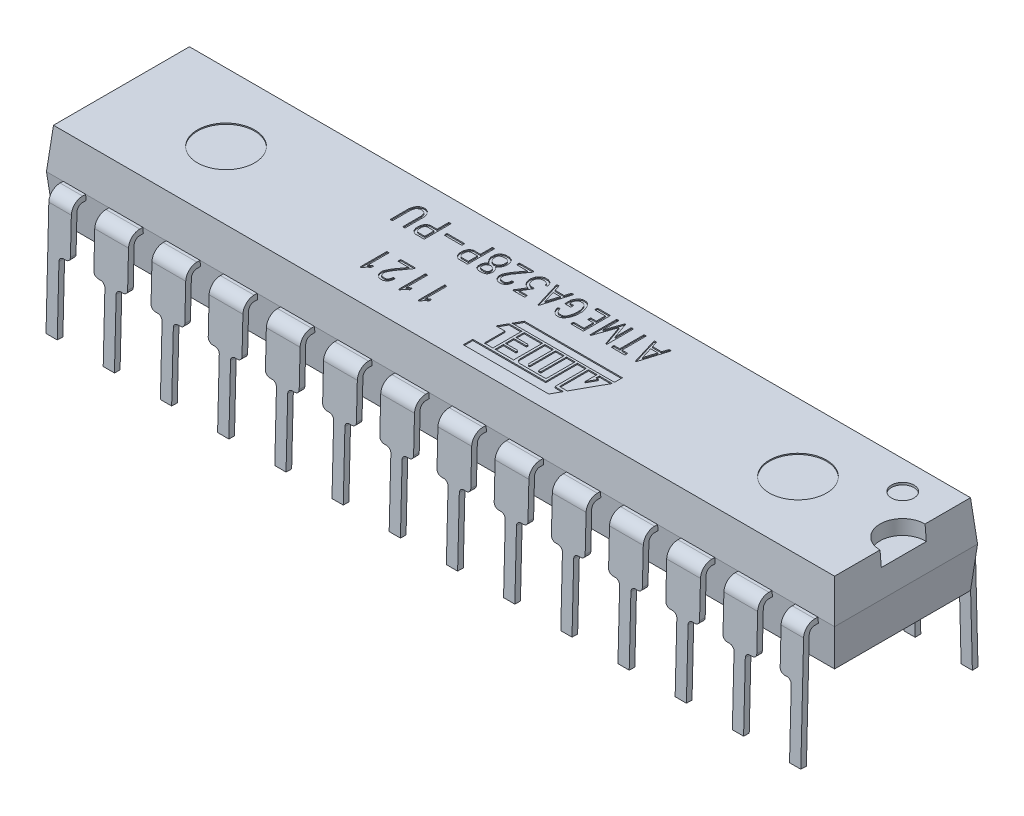
SolidWorks part; units mm, degrees
material "Pure Silver"
ref_plane "Front Plane" through (0, 0, 0) normal (0, 0, 1) x (1, 0, 0)
ref_plane "Top Plane" through (0, 0, 0) normal (0, 1, 0) x (1, 0, 0)
ref_plane "Right Plane" through (0, 0, 0) normal (1, 0, 0) x (0, 0, -1)
sketch "Sketch1" plane through (0, 0, 0) normal (1, 0, 0) x (0, 0, -1)
  line L0 (-3.935, -3.18) -> (-3.81, 1.8075)
  line L1 (-3.3102, 2.295) -> (3.3102, 2.295)
  line L2 (3.81, 1.8075) -> (3.935, -3.18)
  line L4 (55, 0) -> (-55, 0) construction
  line L5 (0, 4.893) -> (0, -4.893) construction
  arc A0 (3.3102, 2.295) -> (3.81, 1.8075) centre (3.3102, 1.795) cw
  arc A1 (-3.81, 1.8075) -> (-3.3102, 2.295) centre (-3.3102, 1.795) cw
  dimension "D1" = 0.5
  dimension "D2" = 7.62
  dimension "D3" = 3.81
  dimension "D4" = 3.18
  dimension "D5" = 2.295
  dimension "D6" = 7.87
  dimension "D7" = 3.935
extrude "Extrude-Thin1" add sketch "Sketch1" along normal mid plane 33.52 thin
sketch "Sketch2" plane through (0, 0, 0) normal (0, 0, 1) x (1, 0, 0)
  line L0 (-3.56, -3.5) -> (-3.56, -0.2)
  line L1 (-6.1, -3.5) -> (-6.1, -0.2)
  line L2 (4.3285, 0) -> (-4.3285, 0) construction
  line L3 (-1.52, -0.2) -> (-1.52, -3.5)
  line L4 (-3.56, -3.5) -> (-1.52, -3.5)
  line L5 (-1.02, -3.5) -> (-1.02, -0.2)
  line L6 (1.02, -0.2) -> (1.02, -3.5)
  line L7 (-1.02, -3.5) -> (1.02, -3.5)
  line L8 (1.52, -3.5) -> (1.52, -0.2)
  line L9 (3.56, -0.2) -> (3.56, -3.5)
  line L10 (1.52, -3.5) -> (3.56, -3.5)
  line L11 (-4.06, -0.2) -> (-4.06, -3.5)
  line L12 (-5.9, 0) -> (-5.8, 0)
  line L13 (0, -3.0147) -> (0, 3.0147) construction
  line L14 (-3.36, 0) -> (-3.26, 0)
  line L15 (-3.06, 0.2) -> (-3.06, 2.295)
  line L16 (16.76, 2.295) -> (-16.76, 2.295) construction
  line L17 (-3.06, 2.295) -> (-2.02, 2.295)
  line L18 (-2.02, 2.295) -> (-2.02, 0.2)
  line L19 (-0.52, 0.2) -> (-0.52, 2.295)
  line L20 (-0.52, 2.295) -> (0.52, 2.295)
  line L21 (0.52, 2.295) -> (0.52, 0.2)
  line L22 (2.02, 0.2) -> (2.02, 2.295)
  line L23 (2.02, 2.295) -> (3.06, 2.295)
  line L24 (3.06, 2.295) -> (3.06, 0.2)
  line L25 (-5.6, 0.2) -> (-5.6, 2.295)
  line L26 (-1.82, 0) -> (-1.72, 0)
  line L27 (-4.56, 2.295) -> (-4.56, 0.2)
  line L28 (-0.82, 0) -> (-0.72, 0)
  line L29 (0.72, 0) -> (0.82, 0)
  line L30 (1.72, 0) -> (1.82, 0)
  line L31 (3.26, 0) -> (3.36, 0)
  line L32 (-4.36, 0) -> (-4.26, 0)
  line L33 (-5.6, 2.295) -> (-4.56, 2.295)
  line L34 (-6.1, -3.5) -> (-4.06, -3.5)
  line L35 (-8.64, -3.5) -> (-8.64, -0.2)
  line L36 (-6.6, -0.2) -> (-6.6, -3.5)
  line L37 (-8.44, 0) -> (-8.34, 0)
  line L38 (-8.14, 0.2) -> (-8.14, 2.295)
  line L39 (-7.1, 2.295) -> (-7.1, 0.2)
  line L40 (-6.9, 0) -> (-6.8, 0)
  line L41 (-8.14, 2.295) -> (-7.1, 2.295)
  line L42 (-8.64, -3.5) -> (-6.6, -3.5)
  line L43 (-11.18, -3.5) -> (-11.18, -0.2)
  line L44 (-9.14, -0.2) -> (-9.14, -3.5)
  line L45 (-10.98, 0) -> (-10.88, 0)
  line L46 (-10.68, 0.2) -> (-10.68, 2.295)
  line L47 (-9.64, 2.295) -> (-9.64, 0.2)
  line L48 (-9.44, 0) -> (-9.34, 0)
  line L49 (-10.68, 2.295) -> (-9.64, 2.295)
  line L50 (-11.18, -3.5) -> (-9.14, -3.5)
  line L51 (-13.72, -3.5) -> (-13.72, -0.2)
  line L52 (-11.68, -0.2) -> (-11.68, -3.5)
  line L53 (-13.52, 0) -> (-13.42, 0)
  line L54 (-13.22, 0.2) -> (-13.22, 2.295)
  line L55 (-12.18, 2.295) -> (-12.18, 0.2)
  line L56 (-11.98, 0) -> (-11.88, 0)
  line L57 (-13.22, 2.295) -> (-12.18, 2.295)
  line L58 (-13.72, -3.5) -> (-11.68, -3.5)
  line L59 (-16.26, -3.5) -> (-16.26, -0.2)
  line L60 (-14.22, -0.2) -> (-14.22, -3.5)
  line L61 (-16.06, 0) -> (-15.96, 0)
  line L62 (-15.76, 0.2) -> (-15.76, 2.295)
  line L63 (-14.72, 2.295) -> (-14.72, 0.2)
  line L64 (-14.52, 0) -> (-14.42, 0)
  line L65 (-15.76, 2.295) -> (-14.72, 2.295)
  line L66 (-16.26, -3.5) -> (-14.22, -3.5)
  line L67 (4.06, -3.5) -> (4.06, -0.2)
  line L68 (6.1, -0.2) -> (6.1, -3.5)
  line L69 (5.8, 0) -> (5.9, 0)
  line L70 (4.26, 0) -> (4.36, 0)
  line L71 (4.56, 0.2) -> (4.56, 2.295)
  line L72 (5.6, 2.295) -> (5.6, 0.2)
  line L73 (4.56, 2.295) -> (5.6, 2.295)
  line L74 (4.06, -3.5) -> (6.1, -3.5)
  line L75 (6.6, -3.5) -> (6.6, -0.2)
  line L76 (8.64, -0.2) -> (8.64, -3.5)
  line L77 (8.34, 0) -> (8.44, 0)
  line L78 (6.8, 0) -> (6.9, 0)
  line L79 (7.1, 0.2) -> (7.1, 2.295)
  line L80 (8.14, 2.295) -> (8.14, 0.2)
  line L81 (7.1, 2.295) -> (8.14, 2.295)
  line L82 (6.6, -3.5) -> (8.64, -3.5)
  line L83 (9.14, -3.5) -> (9.14, -0.2)
  line L84 (11.18, -0.2) -> (11.18, -3.5)
  line L85 (10.88, 0) -> (10.98, 0)
  line L86 (9.34, 0) -> (9.44, 0)
  line L87 (9.64, 0.2) -> (9.64, 2.295)
  line L88 (10.68, 2.295) -> (10.68, 0.2)
  line L89 (9.64, 2.295) -> (10.68, 2.295)
  line L90 (9.14, -3.5) -> (11.18, -3.5)
  line L91 (11.68, -3.5) -> (11.68, -0.2)
  line L92 (13.72, -0.2) -> (13.72, -3.5)
  line L93 (13.42, 0) -> (13.52, 0)
  line L94 (11.88, 0) -> (11.98, 0)
  line L95 (12.18, 0.2) -> (12.18, 2.295)
  line L96 (13.22, 2.295) -> (13.22, 0.2)
  line L97 (12.18, 2.295) -> (13.22, 2.295)
  line L98 (11.68, -3.5) -> (13.72, -3.5)
  line L99 (14.22, -3.5) -> (14.22, -0.2)
  line L100 (16.26, -0.2) -> (16.26, -3.5)
  line L101 (15.96, 0) -> (16.06, 0)
  line L102 (14.42, 0) -> (14.52, 0)
  line L103 (14.72, 0.2) -> (14.72, 2.295)
  line L104 (15.76, 2.295) -> (15.76, 0.2)
  line L105 (14.72, 2.295) -> (15.76, 2.295)
  line L106 (14.22, -3.5) -> (16.26, -3.5)
  line L107 (1.52, -3.5) -> (4.06, -3.5) construction
  arc A0 (-3.56, -0.2) -> (-3.36, 0) centre (-3.36, -0.2) cw
  arc A1 (-1.52, -0.2) -> (-1.72, 0) centre (-1.72, -0.2) ccw
  arc A2 (-1.02, -0.2) -> (-0.82, 0) centre (-0.82, -0.2) cw
  arc A3 (3.56, -0.2) -> (3.36, 0) centre (3.36, -0.2) ccw
  arc A4 (1.52, -0.2) -> (1.72, 0) centre (1.72, -0.2) cw
  arc A5 (1.02, -0.2) -> (0.82, 0) centre (0.82, -0.2) ccw
  arc A6 (-3.26, 0) -> (-3.06, 0.2) centre (-3.26, 0.2) ccw
  arc A7 (-2.02, 0.2) -> (-1.82, 0) centre (-1.82, 0.2) ccw
  arc A8 (3.06, 0.2) -> (3.26, 0) centre (3.26, 0.2) ccw
  arc A9 (2.02, 0.2) -> (1.82, 0) centre (1.82, 0.2) cw
  arc A10 (0.52, 0.2) -> (0.72, 0) centre (0.72, 0.2) ccw
  arc A11 (-0.52, 0.2) -> (-0.72, 0) centre (-0.72, 0.2) cw
  arc A12 (-6.1, -0.2) -> (-5.9, 0) centre (-5.9, -0.2) cw
  arc A13 (-5.8, 0) -> (-5.6, 0.2) centre (-5.8, 0.2) ccw
  arc A14 (-4.56, 0.2) -> (-4.36, 0) centre (-4.36, 0.2) ccw
  arc A15 (-4.06, -0.2) -> (-4.26, 0) centre (-4.26, -0.2) ccw
  arc A16 (-8.64, -0.2) -> (-8.44, 0) centre (-8.44, -0.2) cw
  arc A17 (-8.34, 0) -> (-8.14, 0.2) centre (-8.34, 0.2) ccw
  arc A18 (-7.1, 0.2) -> (-6.9, 0) centre (-6.9, 0.2) ccw
  arc A19 (-6.6, -0.2) -> (-6.8, 0) centre (-6.8, -0.2) ccw
  arc A20 (-11.18, -0.2) -> (-10.98, 0) centre (-10.98, -0.2) cw
  arc A21 (-10.88, 0) -> (-10.68, 0.2) centre (-10.88, 0.2) ccw
  arc A22 (-9.64, 0.2) -> (-9.44, 0) centre (-9.44, 0.2) ccw
  arc A23 (-9.14, -0.2) -> (-9.34, 0) centre (-9.34, -0.2) ccw
  arc A24 (-13.72, -0.2) -> (-13.52, 0) centre (-13.52, -0.2) cw
  arc A25 (-13.42, 0) -> (-13.22, 0.2) centre (-13.42, 0.2) ccw
  arc A26 (-12.18, 0.2) -> (-11.98, 0) centre (-11.98, 0.2) ccw
  arc A27 (-11.68, -0.2) -> (-11.88, 0) centre (-11.88, -0.2) ccw
  arc A28 (-16.26, -0.2) -> (-16.06, 0) centre (-16.06, -0.2) cw
  arc A29 (-15.96, 0) -> (-15.76, 0.2) centre (-15.96, 0.2) ccw
  arc A30 (-14.72, 0.2) -> (-14.52, 0) centre (-14.52, 0.2) ccw
  arc A31 (-14.22, -0.2) -> (-14.42, 0) centre (-14.42, -0.2) ccw
  arc A32 (6.1, -0.2) -> (5.9, 0) centre (5.9, -0.2) ccw
  arc A33 (5.6, 0.2) -> (5.8, 0) centre (5.8, 0.2) ccw
  arc A34 (4.56, 0.2) -> (4.36, 0) centre (4.36, 0.2) cw
  arc A35 (4.06, -0.2) -> (4.26, 0) centre (4.26, -0.2) cw
  arc A36 (8.64, -0.2) -> (8.44, 0) centre (8.44, -0.2) ccw
  arc A37 (8.14, 0.2) -> (8.34, 0) centre (8.34, 0.2) ccw
  arc A38 (7.1, 0.2) -> (6.9, 0) centre (6.9, 0.2) cw
  arc A39 (6.6, -0.2) -> (6.8, 0) centre (6.8, -0.2) cw
  arc A40 (11.18, -0.2) -> (10.98, 0) centre (10.98, -0.2) ccw
  arc A41 (10.68, 0.2) -> (10.88, 0) centre (10.88, 0.2) ccw
  arc A42 (9.64, 0.2) -> (9.44, 0) centre (9.44, 0.2) cw
  arc A43 (9.14, -0.2) -> (9.34, 0) centre (9.34, -0.2) cw
  arc A44 (13.72, -0.2) -> (13.52, 0) centre (13.52, -0.2) ccw
  arc A45 (13.22, 0.2) -> (13.42, 0) centre (13.42, 0.2) ccw
  arc A46 (12.18, 0.2) -> (11.98, 0) centre (11.98, 0.2) cw
  arc A47 (11.68, -0.2) -> (11.88, 0) centre (11.88, -0.2) cw
  arc A48 (16.26, -0.2) -> (16.06, 0) centre (16.06, -0.2) ccw
  arc A49 (15.76, 0.2) -> (15.96, 0) centre (15.96, 0.2) ccw
  arc A50 (14.72, 0.2) -> (14.52, 0) centre (14.52, 0.2) cw
  arc A51 (14.22, -0.2) -> (14.42, 0) centre (14.42, -0.2) cw
  point P35 (-3.56, 0)
  point P40 (-1.52, 0)
  point P43 (-1.02, 0)
  point P46 (3.56, 0)
  point P49 (1.52, 0)
  point P52 (1.02, 0)
  point P55 (-3.06, 0)
  point P58 (-2.02, 0)
  point P61 (3.06, 0)
  point P64 (2.02, 0)
  point P67 (0.52, 0)
  point P70 (-0.52, 0)
  dimension "D7" = 0.2
  dimension "D1" = 0.5
  dimension "D2" = 2.54
  dimension "D3" = 1.52
  dimension "D4" = 1.52
  dimension "D5" = 1.5
  dimension "D6" = 0.5
  dimension "D8" = 3.5
  dimension "D10" = 4.56
  dimension "D12" = 2.54
  dimension "D9" = 6
  dimension "D11" = 6
extrude "Cut-Extrude1" cut sketch "Sketch2" against normal through all and the other way through all
sketch "Sketch3" plane through (0, 0, 0) normal (1, 0, 0) x (0, 0, -1)
  line L0 (0, 4.893) -> (0, -4.893) construction
  line L1 (-3.0188, 4.08) -> (3.0188, 4.08)
  line L2 (-3.3102, 2.295) -> (3.3102, 2.295) construction
  line L3 (-3.0188, 0.51) -> (3.0188, 0.51)
  line L5 (4.3285, 0) -> (-4.3285, 0) construction
  line L6 (-3.175, 2.295) -> (-3.0188, 4.08)
  line L7 (-3.175, 2.295) -> (-3.0188, 0.51)
  line L8 (3.0188, 4.08) -> (3.175, 2.295)
  line L9 (3.175, 2.295) -> (3.0188, 0.51)
  dimension "D1" = 85
  dimension "D2" = 6.35
  dimension "D3" = 4.08
  dimension "D4" = 0.51
  dimension "D5" = 85
  dimension "D6" = 3.175
  dimension "D7" = 3.57
extrude "Boss-Extrude1" add sketch "Sketch3" along normal mid plane 35
sketch "Sketch4" plane through (0, 0, 0) normal (0, 0, 1) x (1, 0, 0)
  line L0 (-17.3438, 4.08) -> (-17.5, 2.295)
  line L1 (17.5, 4.08) -> (-17.5, 4.08) construction
  line L2 (-17.5, 2.295) -> (-17.3438, 0.51)
  line L3 (17.5, 0.51) -> (-17.5, 0.51) construction
  line L4 (17.5, 2.295) -> (17.3438, 4.08)
  line L5 (17.5, 2.295) -> (17.3438, 0.51)
  line L6 (0, -3.0147) -> (0, 3.0147) construction
  line L7 (17.3438, 4.08) -> (20, 4.08)
  line L8 (20, 4.08) -> (20, 0.51)
  line L9 (20, 0.51) -> (17.3438, 0.51)
  line L11 (-17.3438, 4.08) -> (-20, 4.08)
  line L12 (-20, 4.08) -> (-20, 0.51)
  line L13 (-20, 0.51) -> (-17.3438, 0.51)
  dimension "D1" = 5
  dimension "D2" = 5
  dimension "D3" = 40
  dimension "D4" = 20
extrude "Cut-Extrude2" cut sketch "Sketch4" against normal through all and the other way through all
sketch "Sketch5" plane through (0, 4.08, 0) normal (0, 1, 0) x (1, 0, 0)
  line L0 (17.3438, 3.0188) -> (17.3438, -3.0188) construction
  circle A0 centre (17.3438, 0) radius 1
  dimension "D1" = 2
extrude "Cut-Extrude3" cut sketch "Sketch5" against normal blind 0.65
sketch "Sketch6" plane through (0, 4.08, 0) normal (0, 1, 0) x (1, 0, 0)
  line L0 (0.4051, -0.54) -> (0.98, -0.54)
  line L1 (5, -0.45) -> (0.455, -0.45)
  line L2 (0.649, -0.1) -> (0.455, -0.45)
  line L3 (1.08, -0.91) -> (1.61, -0.91)
  line L4 (0.2, -0.91) -> (0.6, -0.91)
  line L5 (1.08, -1) -> (1.61, -1)
  line L6 (1.08, -1.37) -> (1.61, -1.37)
  line L7 (1.08, -1.46) -> (1.61, -1.46)
  line L8 (0.2, -1.94) -> (3.44, -1.94)
  line L9 (0.2, -2.36) -> (3.9912, -2.36)
  line L10 (5, -0.54) -> (4.2849, -1.83)
  line L11 (2.2, -1.83) -> (3.34, -1.83)
  line L12 (4.42, -0.54) -> (4.42, -0.69)
  line L13 (0.649, -0.1) -> (5, -0.1)
  line L14 (5, -0.1) -> (5, -0.45)
  line L15 (4.42, -0.69) -> (4.53, -0.69)
  line L16 (4.53, -0.69) -> (4.32, -1.0689)
  line L17 (4.32, -1.0689) -> (4.32, -0.54)
  line L18 (0.98, -0.54) -> (0.98, -1.83)
  line L19 (1.08, -0.54) -> (1.08, -1.83)
  line L20 (1.9, -0.54) -> (1.9, -1.83)
  line L21 (2, -0.54) -> (2, -1.63)
  line L22 (2.38, -0.54) -> (2.38, -1.63)
  line L23 (2.48, -0.54) -> (2.48, -1.69)
  line L24 (2.86, -0.54) -> (2.86, -1.67)
  line L25 (2.96, -0.54) -> (2.96, -1.67)
  line L26 (3.34, -0.54) -> (3.34, -1.83)
  line L27 (3.44, -0.54) -> (3.44, -1.94)
  line L28 (3.84, -0.54) -> (3.84, -1.94)
  line L29 (3.94, -0.54) -> (3.94, -1.83)
  line L30 (2.94, -1.69) -> (2.88, -1.69)
  line L31 (2.48, -1.69) -> (2.44, -1.69)
  line L32 (1.9, -1.83) -> (1.08, -1.83)
  line L33 (0.6, -0.91) -> (0.6, -1.83)
  line L34 (0.4051, -0.54) -> (0.2, -0.91)
  line L35 (1.64, -0.94) -> (1.64, -0.97)
  line L36 (3.94, -1.83) -> (4.2849, -1.83)
  line L37 (3.84, -1.94) -> (4.224, -1.94)
  line L38 (1.08, -0.54) -> (1.9, -0.54)
  line L39 (2, -0.54) -> (2.38, -0.54)
  line L40 (1.64, -1.4) -> (1.64, -1.43)
  line L41 (0.98, -1.83) -> (0.6, -1.83)
  line L42 (0.2, -1.94) -> (0.2, -2.36)
  line L43 (4.224, -1.94) -> (3.9912, -2.36)
  line L44 (2.48, -0.54) -> (2.86, -0.54)
  line L45 (2.96, -0.54) -> (3.34, -0.54)
  line L46 (3.44, -0.54) -> (3.84, -0.54)
  line L47 (3.94, -0.54) -> (4.32, -0.54)
  line L48 (4.42, -0.54) -> (5, -0.54)
  line L49 (0, -3.9964) -> (0, 3.9964) construction
  line L55 (-4.893, 0) -> (4.893, 0) construction
  arc A0 (2.2, -1.83) -> (2, -1.63) centre (2.2, -1.63) cw
  arc A1 (2.44, -1.69) -> (2.38, -1.63) centre (2.44, -1.63) cw
  arc A2 (2.94, -1.69) -> (2.96, -1.67) centre (2.94, -1.67) ccw
  arc A3 (2.86, -1.67) -> (2.88, -1.69) centre (2.88, -1.67) ccw
  arc A4 (1.61, -1.46) -> (1.64, -1.43) centre (1.61, -1.43) ccw
  arc A5 (1.64, -1.4) -> (1.61, -1.37) centre (1.61, -1.4) ccw
  arc A6 (1.61, -1) -> (1.64, -0.97) centre (1.61, -0.97) ccw
  arc A7 (1.64, -0.94) -> (1.61, -0.91) centre (1.61, -0.94) ccw
  dimension "D25" = 0.2
  dimension "D26" = 0.06
  dimension "D28" = 0.02
  dimension "D33" = 0.03
  dimension "D1" = 0.09
  dimension "D2" = 0.09
  dimension "D3" = 0.09
  dimension "D4" = 0.11
  dimension "D5" = 61
  dimension "D6" = 0.15
  dimension "D7" = 0.11
  dimension "D8" = 0.37
  dimension "D9" = 0.37
  dimension "D10" = 0.37
  dimension "D11" = 0.42
  dimension "D12" = 0.1
  dimension "D13" = 0.1
  dimension "D14" = 0.1
  dimension "D15" = 0.1
  dimension "D16" = 0.1
  dimension "D17" = 0.1
  dimension "D18" = 1.06
  dimension "D19" = 0.4
  dimension "D20" = 0.38
  dimension "D21" = 0.38
  dimension "D22" = 0.38
  dimension "D23" = 0.82
  dimension "D24" = 4.8
  dimension "D27" = 0.14
  dimension "D29" = 0.38
  dimension "D30" = 0.38
  dimension "D31" = 0.1
  dimension "D32" = 0.56
  dimension "D34" = 5
  dimension "D36" = 0.35
  dimension "D37" = 0.1
extrude "Cut-Extrude4" cut sketch "Sketch6" against normal blind 0.05 contours L46 L27 L8 L42 L9 L43 L37 L28 | A3 L24 L44 L23 L31 A1 L22 L39 L21 A0 L11 L26 L45 L25 A2 L30 | L48 L12 L15 L16 L17 L47 L29 L36 L10 | A7 L35 A6 L5 L19 L6 A5 L40 A4 L7 L32 L20 L38 L3 | L41 L18 L0 L34 L4 L33 | L13 L14 L1 L2
sketch "Sketch8" plane through (0, 4.08, 0) normal (0, 1, 0) x (1, 0, 0)
  line L0 (-2, -0.5) -> (-6.7038, -0.5) construction
  line L1 (5.1, 2) -> (-7.2875, 2) construction
  line L2 (-4.893, 0) -> (4.893, 0) construction
  line L3 (0, -3.9964) -> (0, 3.9964) construction
  text T0 "1121" font "SWRomnd" height 1.2
  text T1 "ATMEGA328P-PU" font "SWRomnd" height 1.2
  dimension "D1" = 2
  dimension "D2" = 0.5
  dimension "D3" = 2
  dimension "D4" = 5.1
extrude "Cut-Extrude5" cut sketch "Sketch8" against normal blind 0.05
sketch "Sketch9" plane through (0, 4.08, 0) normal (0, 1, 0) x (1, 0, 0)
  line L0 (-4.893, 0) -> (4.893, 0) construction
  line L1 (0, -3.9964) -> (0, 3.9964) construction
  circle A0 centre (-12.7, 0) radius 1.27
  circle A1 centre (12.7, 0) radius 1.27
  dimension "D1" = 2.54
  dimension "D2" = 12.7
  dimension "D3" = 12.7
extrude "Cut-Extrude6" cut sketch "Sketch9" against normal blind 0.05
sketch "Sketch10" plane through (0, 4.08, 0) normal (0, 1, 0) x (1, 0, 0)
  line L0 (0, -3.9964) -> (0, 3.9964) construction
  line L1 (-4.893, 0) -> (4.893, 0) construction
  circle A0 centre (15.6, 1.75) radius 0.5
  dimension "D1" = 1
  dimension "D2" = 15.6
  dimension "D3" = 1.75
extrude "Cut-Extrude7" cut sketch "Sketch10" against normal blind 0.1
